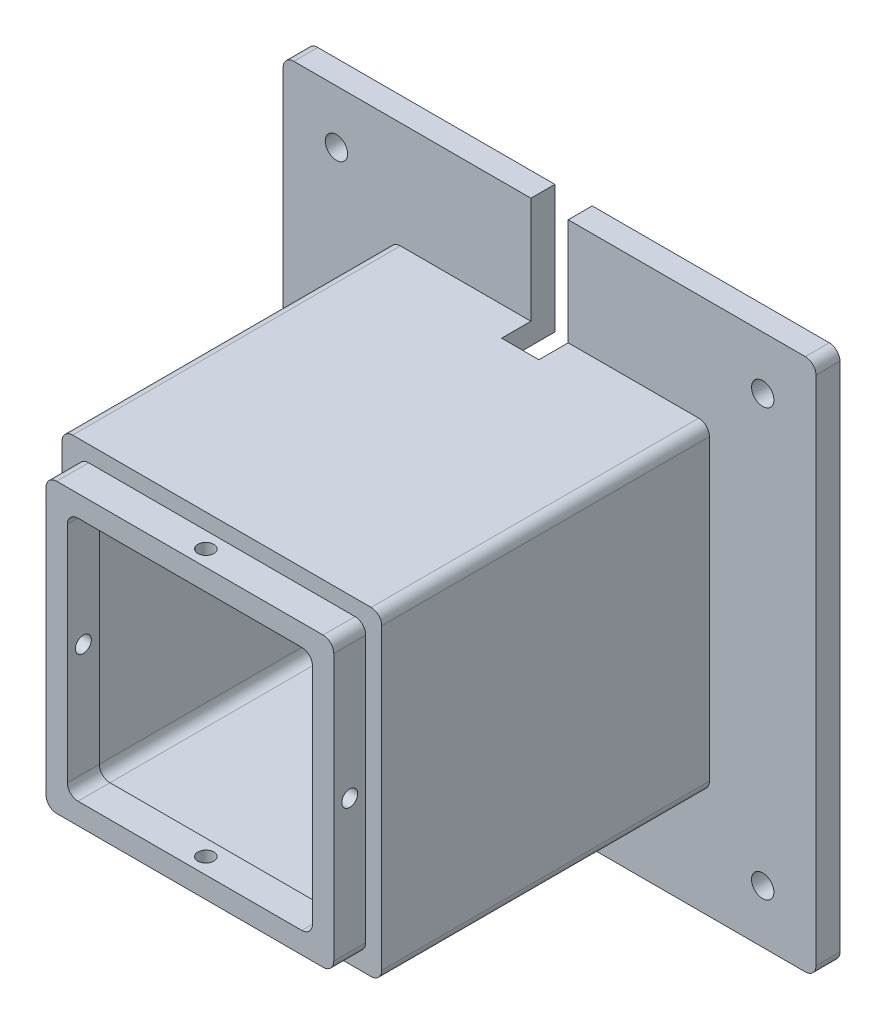
SolidWorks part; units mm, degrees
ref_plane "前视基准面" through (0, 0, 0) normal (0, 0, 1) x (1, 0, 0)
ref_plane "上视基准面" through (0, 0, 0) normal (0, 1, 0) x (1, 0, 0)
ref_plane "右视基准面" through (0, 0, 0) normal (1, 0, 0) x (0, 0, -1)
sketch "草图1" plane through (0, 0, 0) normal (0, 0, 1) x (1, 0, 0)
  line L1 (-30, 30) -> (30, 30)
  line L2 (-30, 30) -> (-30, -30)
  line L3 (-30, -30) -> (30, -30)
  line L4 (30, 30) -> (30, -30)
  line L5 (-30, 30) -> (30, -30) construction
  line L6 (-30, -30) -> (30, 30) construction
  point P0 (0, 0)
extrude "凸台-拉伸1" add sketch "草图1" along normal blind 55.5 contours L2 L1 L4 L3
sketch "草图2" plane through (0, 0, 55.5) normal (0, 0, 1) x (1, 0, 0)
  line L1 (-25, 25) -> (25, 25)
  line L2 (-25, 25) -> (-25, -25)
  line L3 (-25, -25) -> (25, -25)
  line L4 (25, 25) -> (25, -25)
  line L5 (-25, 25) -> (25, -25) construction
  line L6 (-25, -25) -> (25, 25) construction
  point P0 (0, 0)
extrude "切除-拉伸3" cut sketch "草图2" against normal blind 49.5
sketch "草图4" plane through (0, 0, 0) normal (0, 0, -1) x (-1, 0, 0)
  line L1 (-19.2, 19.2) -> (19.2, 19.2)
  line L2 (-19.2, 19.2) -> (-19.2, -19.2)
  line L3 (-19.2, -19.2) -> (19.2, -19.2)
  line L4 (19.2, 19.2) -> (19.2, -19.2)
  line L5 (-19.2, 19.2) -> (19.2, -19.2) construction
  line L6 (-19.2, -19.2) -> (19.2, 19.2) construction
  point P0 (0, 0)
extrude "切除-拉伸4" cut sketch "草图4" against normal blind 4
sketch "草图5" plane through (0, 0, 4) normal (0, 0, -1) x (-1, 0, 0)
  line L1 (-19.2, 19.2) -> (-11.2, 19.2)
  line L2 (-19.2, 19.2) -> (-19.2, 11.2)
  line L3 (-19.2, 11.2) -> (-11.2, 11.2)
  line L4 (-11.2, 19.2) -> (-11.2, 11.2)
  line L5 (19.2, 19.2) -> (11.2, 19.2)
  line L6 (19.2, 19.2) -> (19.2, 11.2)
  line L7 (19.2, 11.2) -> (11.2, 11.2)
  line L8 (11.2, 19.2) -> (11.2, 11.2)
  line L9 (19.2, -19.2) -> (11.2, -19.2)
  line L10 (19.2, -19.2) -> (19.2, -11.2)
  line L11 (19.2, -11.2) -> (11.2, -11.2)
  line L12 (11.2, -19.2) -> (11.2, -11.2)
  line L13 (-19.2, -19.2) -> (-11.2, -19.2)
  line L14 (-19.2, -19.2) -> (-19.2, -11.2)
  line L15 (-19.2, -11.2) -> (-11.2, -11.2)
  line L16 (-11.2, -19.2) -> (-11.2, -11.2)
extrude "凸台-拉伸3" add sketch "草图5" along normal blind 2.5
sketch "草图6" plane through (0, 0, 1.5) normal (0, 0, -1) x (-1, 0, 0)
  circle A0 centre (-14, 14) radius 1.25
  circle A1 centre (14, 14) radius 1.25
  circle A2 centre (-14, -14) radius 1.25
  circle A3 centre (13.9975, -14.0344) radius 1.25
extrude "切除-拉伸5" cut sketch "草图6" against normal up to next
sketch "草图7" plane through (0, 0, 4) normal (0, 0, -1) x (-1, 0, 0)
  circle A0 centre (0, 0) radius 11.5
extrude "切除-拉伸6" cut sketch "草图7" against normal blind 2.5 contours A0
fillet "圆角5" radius 1 12 edges at (-11.2, -19.2, 2.75) (-19.2, -11.2, 2.75) (-11.2, -11.2, 2.75) (11.2, -19.2, 2.75) (19.2, -11.2, 2.75) (11.2, -11.2, 2.75) (19.2, 11.2, 2.75) (11.2, 11.2, 2.75) (11.2, 19.2, 2.75) (-19.2, 11.2, 2.75) (-11.2, 19.2, 2.75) (-11.2, 11.2, 2.75)
sketch "草图12" plane through (0, 0, 55.5) normal (0, 0, 1) x (1, 0, 0)
  line L1 (30, 30) -> (-30, 30)
  line L2 (30, 30) -> (30, -30)
  line L3 (30, -30) -> (-30, -30)
  line L4 (-30, 30) -> (-30, -30)
extrude "切除-拉伸9" cut sketch "草图12" against normal blind 3
sketch "草图17" plane through (0, 0, 0) normal (0, 0, -1) x (-1, 0, 0)
  line L1 (-30, 30) -> (30, 30)
  line L2 (-30, 30) -> (-30, -30)
  line L3 (-30, -30) -> (30, -30)
  line L4 (30, 30) -> (30, -30)
extrude "凸台-拉伸5" add sketch "草图17" along normal blind 13.5
sketch "草图20" plane through (0, 0, 52.5) normal (0, 0, 1) x (1, 0, 0)
  line L1 (-27, 27) -> (27, 27)
  line L2 (-27, 27) -> (-27, -27)
  line L3 (-27, -27) -> (27, -27)
  line L4 (27, 27) -> (27, -27)
  line L5 (-27, 27) -> (27, -27) construction
  line L6 (-27, -27) -> (27, 27) construction
  point P0 (0, 0)
extrude "凸台-拉伸6" add sketch "草图20" along normal blind 6 contours L2 L1 L4 L3
sketch "草图21" plane through (0, 0, 58.5) normal (0, 0, 1) x (1, 0, 0)
  line L1 (-23, 23) -> (23, 23)
  line L2 (-23, 23) -> (-23, -23)
  line L3 (-23, -23) -> (23, -23)
  line L4 (23, 23) -> (23, -23)
  line L5 (-23, 23) -> (23, -23) construction
  line L6 (-23, -23) -> (23, 23) construction
  point P0 (0, 0)
extrude "切除-拉伸18" cut sketch "草图21" against normal blind 6
fillet "圆角9" radius 2 8 edges at (-25, -25, 29.25) (-23, -23, 55.5) (-23, 23, 55.5) (-25, 25, 29.25) (25, -25, 29.25) (23, -23, 55.5) (25, 25, 29.25) (23, 23, 55.5)
fillet "圆角10" radius 2 4 edges at (-27, -27, 55.5) (-27, 27, 55.5) (27, 27, 55.5) (27, -27, 55.5)
sketch "草图24" plane through (0, 0, -13.5) normal (0, 0, -1) x (-1, 0, 0)
  line L1 (-26, 26) -> (26, 26)
  line L2 (-26, 26) -> (-26, -26)
  line L3 (-26, -26) -> (26, -26)
  line L4 (26, 26) -> (26, -26)
  line L5 (-26, 26) -> (26, -26) construction
  line L6 (-26, -26) -> (26, 26) construction
  point P0 (0, 0)
extrude "切除-拉伸21" cut sketch "草图24" against normal blind 13.5
sketch "草图25" plane through (0, 30, 0) normal (0, 1, 0) x (1, 0, 0)
  line L0 (-30, 13.5) -> (30, 13.5) construction
  line L1 (-3.5, 23.5) -> (3.5, 23.5)
  line L2 (-3.5, 23.5) -> (-3.5, 3.5)
  line L3 (-3.5, 3.5) -> (3.5, 3.5)
  line L4 (3.5, 23.5) -> (3.5, 3.5)
  line L5 (-3.5, 23.5) -> (3.5, 3.5) construction
  line L6 (-3.5, 3.5) -> (3.5, 23.5) construction
  point P0 (0, 13.5)
extrude "切除-拉伸22" cut sketch "草图25" against normal up to next
sketch "草图26" plane through (0, 0, -13.5) normal (0, 0, -1) x (-1, 0, 0)
  line L3 (-31.5, -50) -> (-50, -50)
  line L4 (-50, 31.5) -> (-50, -50)
  line L5 (30, 46.5) -> (30, 13.5) construction
  line L8 (-31.5, -50) -> (50, -50)
  line L9 (50, -31.5) -> (50, -50)
  line L11 (50, -31.5) -> (50, 50)
  line L12 (50, 50) -> (30, 50)
  line L16 (-50, 31.5) -> (-50, 50)
  line L17 (-50, 50) -> (30, 50)
extrude "凸台-拉伸7" add sketch "草图26" against normal blind 4.5
sketch "草图27" plane through (0, 0, -13.5) normal (0, 0, -1) x (-1, 0, 0)
  line L1 (-26, 26) -> (26, 26)
  line L2 (-26, 26) -> (-26, -26)
  line L3 (-26, -26) -> (26, -26)
  line L4 (26, 26) -> (26, -26)
  line L5 (-26, 26) -> (26, -26) construction
  line L6 (-26, -26) -> (26, 26) construction
  point P0 (0, 0)
extrude "切除-拉伸24" cut sketch "草图27" against normal blind 4.5
sketch "草图28" plane through (0, 0, -13.5) normal (0, 0, -1) x (-1, 0, 0)
  line L0 (26, 26) -> (-26, 26) construction
  line L1 (-3.5, 50) -> (3.5, 50)
  line L5 (-3.5, 50) -> (-3.5, 26)
  line L6 (26, 26) -> (-26, 26) construction
  line L7 (-3.5, 26) -> (3.5, 26)
  line L8 (3.5, 26) -> (3.5, 50)
  point P0 (0, 26)
extrude "切除-拉伸25" cut sketch "草图28" against normal blind 4.5
sketch "草图29" plane through (0, 0, -13.5) normal (0, 0, -1) x (-1, 0, 0)
  circle A0 centre (-40, 40) radius 2.1
  circle A1 centre (40, 40) radius 2.1
  circle A2 centre (40, -40) radius 2.1
  circle A3 centre (-40, -40) radius 2.1
  point P0 (0, 0)
extrude "切除-拉伸26" cut sketch "草图29" against normal up to next
fillet "圆角12" radius 2 4 edges at (-30, 30, 21.75) (30, 30, 21.75) (30, -30, 21.75) (-30, -30, 21.75)
sketch "草图30" plane through (-27, 0, 0) normal (-1, 0, 0) x (0, 0, 1)
  circle A0 centre (55.5, 0) radius 1.5
extrude "切除-拉伸27" cut sketch "草图30" against normal through all both and the other way through all contours A0
sketch "草图31" plane through (0, 27, 0) normal (0, 1, 0) x (1, 0, 0)
  circle A0 centre (0, -55.5) radius 1.5
extrude "切除-拉伸28" cut sketch "草图31" against normal through all both and the other way through all
fillet "圆角13" radius 2 4 edges at (26, 26, -6.75) (26, -26, -6.75) (-26, -26, -6.75) (-26, 26, -6.75)
fillet "圆角14" radius 2 4 edges at (50, 50, -11.25) (50, -50, -11.25) (-50, -50, -11.25) (-50, 50, -11.25)
